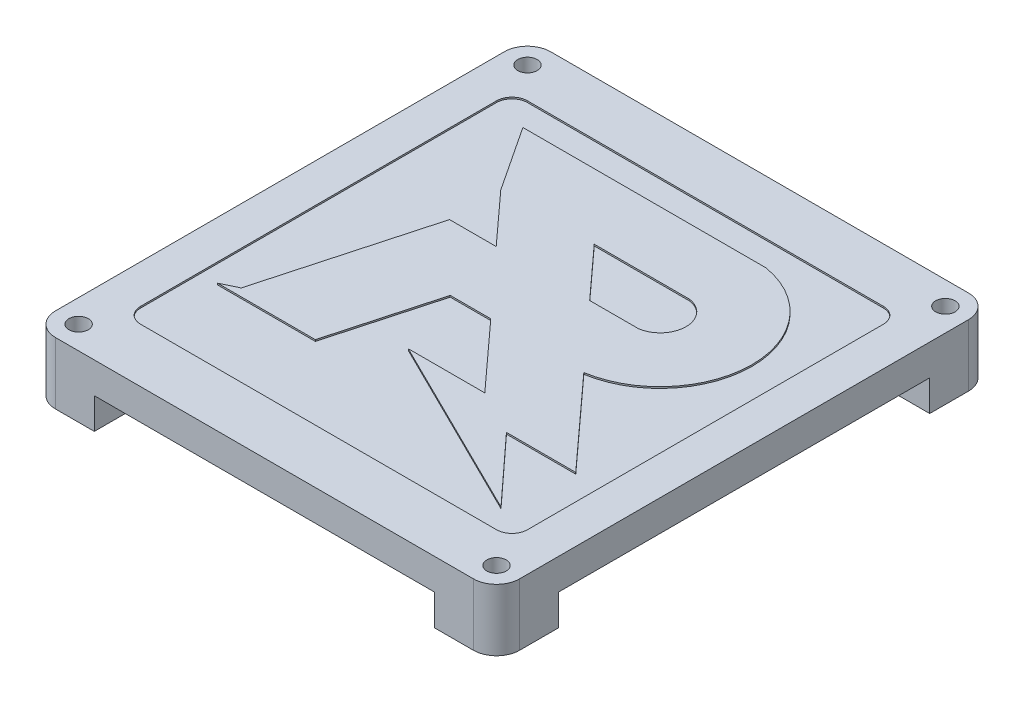
SolidWorks part; units mm, degrees
material "纯银"
ref_plane "前视基准面" through (0, 0, 0) normal (0, 0, 1) x (1, 0, 0)
ref_plane "上视基准面" through (0, 0, 0) normal (0, 1, 0) x (1, 0, 0)
ref_plane "右视基准面" through (0, 0, 0) normal (1, 0, 0) x (0, 0, -1)
other "Configuration Table"
sketch "草图1" plane through (0, 0, 0) normal (0, 1, 0) x (1, 0, 0)
  line L8 (-27.0001, -31.9874) -> (27.0001, -31.9874)
  line L9 (29.9874, -29.0001) -> (29.9874, 29.0001)
  line L10 (27.0001, 31.9874) -> (-27.0001, 31.9874)
  line L11 (-29.9874, 29.0001) -> (-29.9874, -29.0001)
  line L12 (-27.0001, -31.9874) -> (27.0001, -31.9874)
  line L13 (29.9874, -29.0001) -> (29.9874, 29.0001)
  line L14 (27.0001, 31.9874) -> (-27.0001, 31.9874)
  line L15 (-29.9874, 29.0001) -> (-29.9874, -29.0001)
  arc A4 (27.0001, -31.9874) -> (29.9874, -29.0001) centre (27.0001, -29.0001) ccw
  arc A5 (29.9874, 29.0001) -> (27.0001, 31.9874) centre (27.0001, 29.0001) ccw
  arc A6 (-27.0001, 31.9874) -> (-29.9874, 29.0001) centre (-27.0001, 29.0001) ccw
  arc A7 (-29.9874, -29.0001) -> (-27.0001, -31.9874) centre (-27.0001, -29.0001) ccw
  arc A8 (27.0001, -31.9874) -> (29.9874, -29.0001) centre (27.0001, -29.0001) ccw
  arc A9 (29.9874, 29.0001) -> (27.0001, 31.9874) centre (27.0001, 29.0001) ccw
  arc A10 (-27.0001, 31.9874) -> (-29.9874, 29.0001) centre (-27.0001, 29.0001) ccw
  arc A11 (-29.9874, -29.0001) -> (-27.0001, -31.9874) centre (-27.0001, -29.0001) ccw
  dimension "D1" = 0
extrude "凸台-拉伸1" add sketch "草图1" along normal blind 4
sketch "草图2" plane through (0, 0, 0) normal (0, -1, 0) x (1, 0, 0)
  line L1 (27.0001, -31.9874) -> (-27.0001, -31.9874) construction
  line L2 (21.9874, 23.9874) -> (29.9874, 23.9874)
  line L3 (27.0001, -31.9874) -> (21.9874, -31.9874)
  line L4 (-21.9874, 23.9874) -> (-21.9874, 31.9874)
  line L5 (-21.9874, 31.9874) -> (-27.0001, 31.9874)
  line L6 (-29.9874, 29.0001) -> (-29.9874, 23.9874)
  line L7 (-29.9874, 23.9874) -> (-21.9874, 23.9874)
  line L8 (-21.9874, 23.9874) -> (-21.9874, 31.9874)
  line L9 (-21.9874, 31.9874) -> (-27.0001, 31.9874)
  line L10 (-29.9874, 29.0001) -> (-29.9874, 23.9874)
  line L11 (-29.9874, 23.9874) -> (-21.9874, 23.9874)
  line L14 (29.9874, -23.9874) -> (21.9874, -23.9874)
  line L20 (21.9874, 23.9874) -> (29.9874, 23.9874)
  line L21 (29.9874, 23.9874) -> (29.9874, 29.0001)
  line L22 (27.0001, 31.9874) -> (21.9874, 31.9874)
  line L23 (21.9874, 31.9874) -> (21.9874, 23.9874)
  line L26 (27.0001, 31.9874) -> (21.9874, 31.9874)
  line L27 (21.9874, 31.9874) -> (21.9874, 23.9874)
  line L28 (-29.9874, -23.9874) -> (-29.9874, -29.0001)
  line L29 (-21.9874, -23.9874) -> (-29.9874, -23.9874)
  line L30 (-21.9874, -31.9874) -> (-21.9874, -23.9874)
  line L31 (-27.0001, -31.9874) -> (-21.9874, -31.9874)
  line L32 (-29.9874, -23.9874) -> (-29.9874, -29.0001)
  line L33 (-21.9874, -23.9874) -> (-29.9874, -23.9874)
  line L34 (-21.9874, -31.9874) -> (-21.9874, -23.9874)
  line L36 (21.9874, -23.9874) -> (21.9874, -31.9874)
  line L37 (-21.9874, -31.9874) -> (-27.0001, -31.9874)
  line L39 (29.9874, 29.0001) -> (29.9874, -29.0001) construction
  line L40 (29.9874, 23.9874) -> (29.9874, 29.0001)
  line L41 (29.9874, -23.9874) -> (29.9874, -29.0001)
  arc A0 (27.0001, -31.9874) -> (29.9874, -29.0001) centre (27.0001, -29.0001) ccw construction
  arc A1 (-27.0001, 31.9874) -> (-29.9874, 29.0001) centre (-27.0001, 29.0001) ccw
  arc A2 (-27.0001, 31.9874) -> (-29.9874, 29.0001) centre (-27.0001, 29.0001) ccw
  arc A5 (29.9874, 29.0001) -> (27.0001, 31.9874) centre (27.0001, 29.0001) ccw
  arc A6 (29.9874, 29.0001) -> (27.0001, 31.9874) centre (27.0001, 29.0001) ccw
  arc A7 (-29.9874, -29.0001) -> (-27.0001, -31.9874) centre (-27.0001, -29.0001) ccw
  arc A8 (-29.9874, -29.0001) -> (-27.0001, -31.9874) centre (-27.0001, -29.0001) ccw
  arc A9 (27.0001, -31.9874) -> (29.9874, -29.0001) centre (27.0001, -29.0001) ccw
  dimension "D1" = 0
  dimension "D3" = 0
  dimension "D4" = 0
extrude "凸台-拉伸2" add sketch "草图2" along normal blind 4
sketch "草图3" plane through (0, -4, 0) normal (0, -1, 0) x (1, 0, 0)
  circle A0 centre (-27.0001, 29.0001) radius 1.25
  circle A1 centre (27.0001, 29.0001) radius 1.25
  circle A2 centre (27.0001, -29.0001) radius 1.25
  circle A3 centre (-27.0001, -29.0001) radius 1.25
  dimension "D1" = 2.5
  dimension "D2" = 2.5
  dimension "D3" = 2.5
  dimension "D4" = 2.5
extrude "切除-拉伸1" cut sketch "草图3" against normal blind 15
sketch "草图5" plane through (0, 4, 0) normal (0, 1, 0) x (1, 0, 0)
  line L0 (-20.5526, -14.4398) -> (-22.6088, -15.4326)
  line L1 (-9.9755, -15.4235) -> (-9.978, -15.4326)
  line L2 (-9.9755, -15.4235) -> (-6.2161, -1.7651)
  line L3 (-6.2161, -1.7651) -> (-0.9763, -1.7651)
  line L4 (-0.9763, -1.7651) -> (6.9299, -10.4452)
  line L5 (6.9299, -10.4452) -> (-2.9581, -10.4452)
  line L6 (-2.9581, -10.4452) -> (20.6107, -22.0976)
  line L7 (20.6107, -22.0976) -> (20.6747, -22.1293)
  line L8 (20.6747, -22.1293) -> (20.7383, -22.1607)
  line L9 (20.7383, -22.1607) -> (12.7478, -13.4649)
  line L10 (12.7478, -13.4649) -> (21.7014, -13.4649)
  line L11 (21.7014, -13.4649) -> (11.0522, -1.7703)
  line L12 (3.3676, 6.6687) -> (-2.6423, 13.2685)
  line L13 (-2.6423, 13.2685) -> (9.6942, 13.2685)
  line L14 (3.3676, 6.6687) -> (9.6942, 6.6687)
  line L15 (-9.978, -15.4326) -> (-22.6088, -15.4326)
  line L16 (-20.5526, -14.4398) -> (-14.7427, 6.6687)
  line L17 (-14.7427, 6.6687) -> (-8.7108, 6.6687)
  line L18 (-8.7108, 6.6687) -> (-14.7427, 13.291)
  line L19 (-14.7427, 13.291) -> (-20.3091, 21.7161)
  line L20 (-20.3091, 21.7161) -> (11.0836, 21.7161)
  line L22 (-23, -25) -> (23, -25)
  line L23 (-25, -23) -> (-25, 23)
  line L24 (-23, 25) -> (23, 25)
  line L25 (25, -23) -> (25, 23)
  line L26 (0, 25) -> (0, -25) construction
  line L27 (-25, 0) -> (25, 0) construction
  arc A0 (11.0836, 21.7161) -> (11.0522, -1.7703) centre (9.1311, 9.9755) cw
  arc A1 (9.6942, 13.2685) -> (9.6942, 6.6687) centre (9.1879, 9.9686) cw
  arc A2 (-23, -25) -> (-25, -23) centre (-23, -23) cw
  arc A3 (25, 23) -> (23, 25) centre (23, 23) ccw
  arc A4 (25, -23) -> (23, -25) centre (23, -23) cw
  arc A5 (-23, 25) -> (-25, 23) centre (-23, 23) ccw
  point P25 (0, 0)
  point P31 (-25, -25)
  point P41 (-25, 25)
  dimension "D2" = 2
  dimension "D1" = 50
extrude "切除-拉伸2" cut sketch "草图5" against normal blind 0.2 contours L24 A5 L23 A2 L22 A4 L25 A3 L20 A0 L11 L10 L9 L8 L7 L6 L5 L4 L3 L2 L1 L15 L0 L16 L17 L18 L19 | L12 L13 A1 L14
